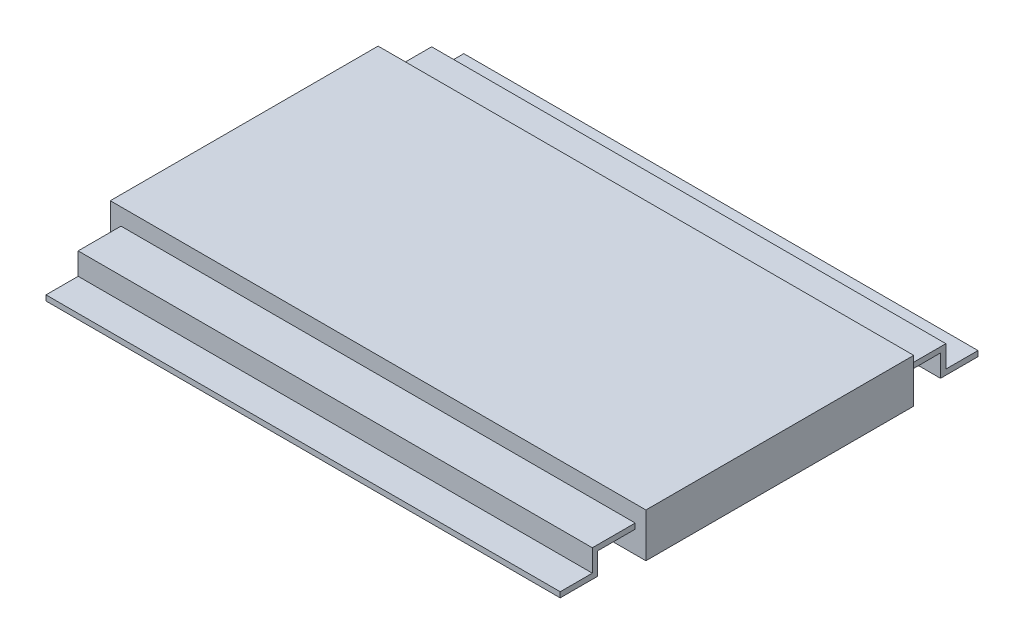
SolidWorks part; units mm, degrees
ref_plane "Front Plane" through (0, 0, 0) normal (0, 0, 1) x (1, 0, 0)
ref_plane "Top Plane" through (0, 0, 0) normal (0, 1, 0) x (1, 0, 0)
ref_plane "Right Plane" through (0, 0, 0) normal (1, 0, 0) x (0, 0, -1)
sketch "Sketch1" plane through (0, 0, 0) normal (1, 0, 0) x (0, 0, -1)
  line L1 (-3.175, 1.044) -> (3.175, 1.044)
  line L2 (-3.175, 1.044) -> (-3.175, 0)
  line L3 (-3.175, 0) -> (3.175, 0)
  line L4 (3.175, 1.044) -> (3.175, 0)
  point P4 (0, 0)
  dimension "D1" = 6.35
  dimension "D2" = 1.044
extrude "Boss-Extrude1" add sketch "Sketch1" along normal mid plane 12.7
sketch "Sketch2" plane through (0, 0, 0) normal (1, 0, 0) x (0, 0, -1)
  line L0 (3.175, 0.522) -> (4.064, 0.522)
  line L1 (4.064, 0.522) -> (4.064, 0)
  line L2 (4.064, 0) -> (4.953, 0)
  line L3 (3.175, 0) -> (3.175, 1.044) construction
  line L4 (-3.175, 0) -> (3.175, 0) construction
  point P8 (3.175, 0.522)
  dimension "D1" = 1.778
extrude "Extrude-Thin1" add sketch "Sketch2" along normal mid plane 12.192 thin thin type one direction reverse wall 0.127
mirror "Mirror1" about plane through (0, 0, 0) normal (0, 0, 1) of "Extrude-Thin1"
